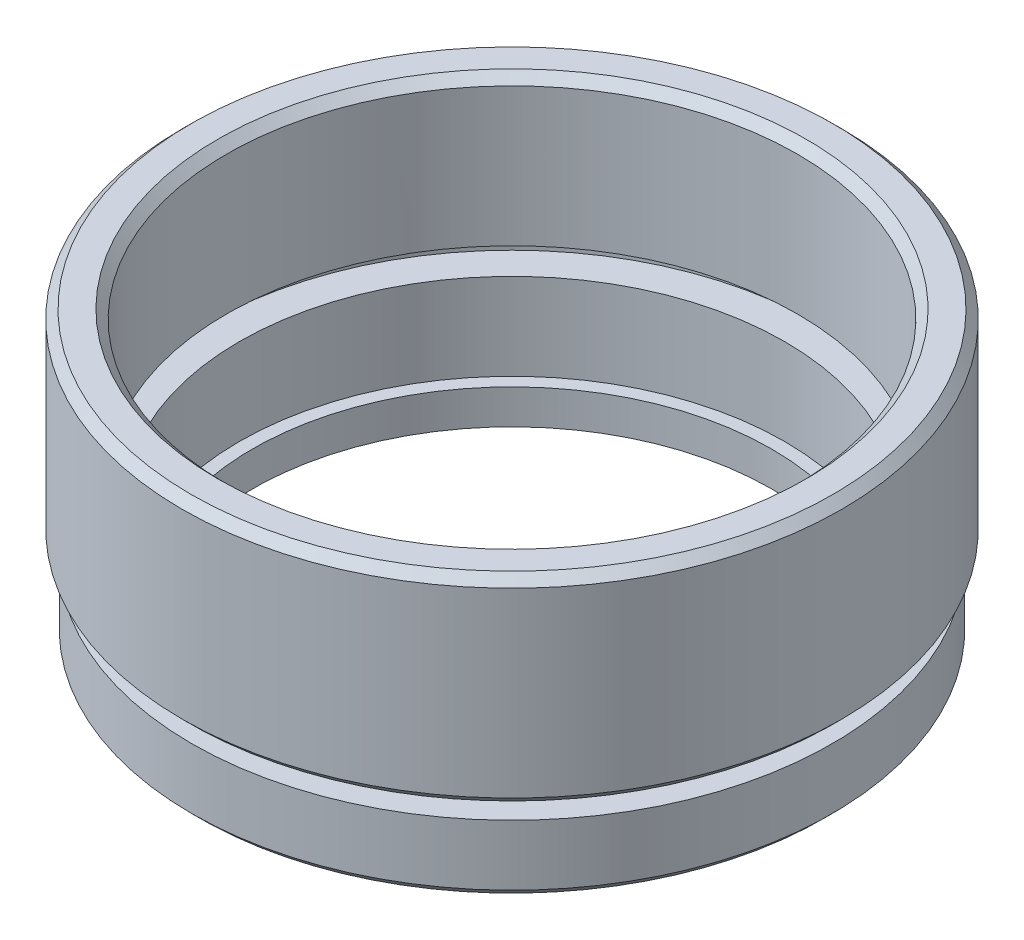
SolidWorks part; units mm, degrees
ref_plane "前视基准面" through (0, 0, 0) normal (0, 0, 1) x (1, 0, 0)
ref_plane "上视基准面" through (0, 0, 0) normal (0, 1, 0) x (1, 0, 0)
ref_plane "右视基准面" through (0, 0, 0) normal (1, 0, 0) x (0, 0, -1)
sketch "草图1" plane through (0, 0, 0) normal (0, 0, 1) x (1, 0, 0)
  line L0 (0, 0) -> (0, 21.8535) construction
  line L1 (15, 0) -> (18.5, 0)
  line L2 (18.5, 0) -> (18.5, 4)
  line L3 (18.5, 4) -> (17, 4)
  line L4 (17, 4) -> (17, 5)
  line L5 (17, 5) -> (19.05, 5)
  line L6 (19.05, 5) -> (19.05, 16.5)
  line L7 (19.05, 16.5) -> (16.5, 16.5)
  line L8 (16.5, 16.5) -> (16.5, 8)
  line L9 (16.5, 8) -> (17.6, 8)
  line L10 (17.6, 8) -> (17.6, 7)
  line L11 (17.6, 7) -> (15.75, 7)
  line L12 (15.75, 7) -> (15.75, 2)
  line L13 (15.75, 2) -> (15, 2)
  line L14 (15, 0) -> (15, 2)
  dimension "D1" = 16.5
  dimension "D2" = 19.05
  dimension "D3" = 16.5
  dimension "D4" = 15.75
  dimension "D5" = 1
  dimension "D6" = 5
  dimension "D7" = 15
  dimension "D8" = 18.5
  dimension "D9" = 1
  dimension "D10" = 5
  dimension "D11" = 2
  dimension "D12" = 17.6
  dimension "D13" = 17
revolve "旋转1" add sketch "草图1" angle 360 about L0
cosmetic thread "装饰螺纹线11"
cosmetic thread "装饰螺纹线12"
chamfer "倒角1" distance 0.5 angle 45 4 edges at (0, 16.5, -16.5) (0, 16.5, -19.05) (0, 5, -19.05) (0, 0, -18.5)
